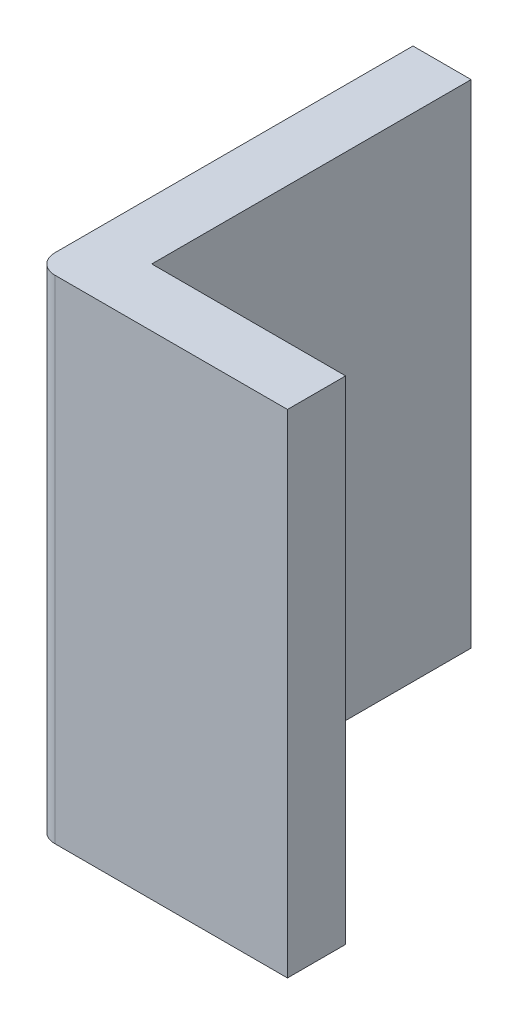
SolidWorks part; units mm, degrees
ref_plane "Plan de face" through (0, 0, 0) normal (0, 0, 1) x (1, 0, 0)
ref_plane "Plan de dessus" through (0, 0, 0) normal (0, 1, 0) x (1, 0, 0)
ref_plane "Plan de droite" through (0, 0, 0) normal (1, 0, 0) x (0, 0, -1)
sketch "Esquisse1" plane through (0, 0, 0) normal (0, 1, 0) x (1, 0, 0)
  line L0 (0, 0) -> (0, 1.6474)
  line L1 (0, 0) -> (1, 0)
  line L2 (-0.3, -0.2) -> (-0.3, 1.6474)
  line L3 (-0.2, -0.3) -> (1, -0.3)
  line L4 (-0.3, 1.6474) -> (0, 1.6474)
  line L5 (1, 0) -> (1, -0.3)
  line L6 (-0.3, -0.3) -> (1, -0.3) construction
  line L7 (-0.3, -0.3) -> (-0.3, 1.6474) construction
  arc A0 (-0.2, -0.3) -> (-0.3, -0.2) centre (-0.2, -0.2) cw
  dimension "D2" = 0.1
  dimension "D1" = 0.3
extrude "Boss.-Extru.1" add sketch "Esquisse1" along normal blind 2.54
